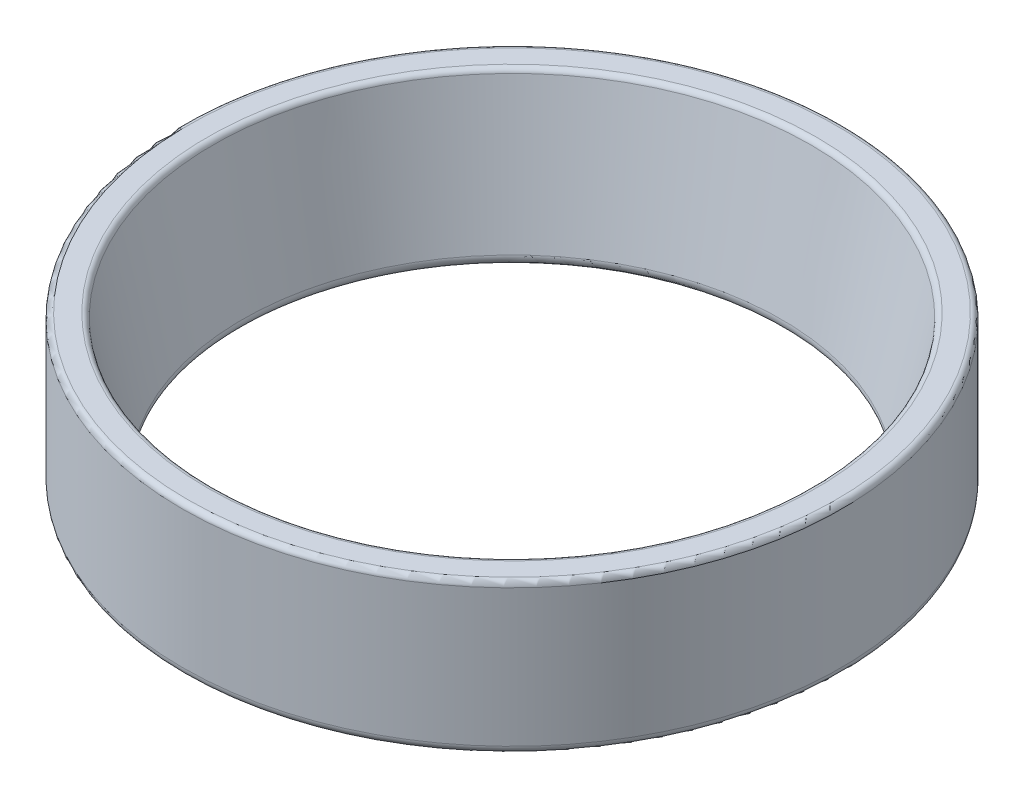
SolidWorks part; units mm, degrees
ref_plane "Front Plane" through (0, 0, 0) normal (0, 0, 1) x (1, 0, 0)
ref_plane "Top Plane" through (0, 0, 0) normal (0, 1, 0) x (1, 0, 0)
ref_plane "Right Plane" through (0, 0, 0) normal (1, 0, 0) x (0, 0, -1)
sketch "Sketch2" plane through (0, 0, 0) normal (0, 0, 1) x (1, 0, 0)
  line L0 (0, 0) -> (-30.5, 0) construction
  line L1 (0, 0) -> (0, 30.8179) construction
  line L2 (-30.5, 0) -> (-30.5, 14)
  line L3 (-30.5, 14) -> (-27.75, 14)
  line L4 (-27.75, 14) -> (-24.75, 0)
  line L5 (-30.5, 0) -> (-24.75, 0)
  dimension "D1" = 14
  dimension "D2" = 2.75
  dimension "D3" = 30.5
  dimension "D4" = 5.75
revolve "Revolve1" add sketch "Sketch2" angle 360 about L1
fillet "Fillet1" radius 0.5 2 edges at (0, 14, -30.5) (0, 14, -27.75)
fillet "Fillet3" radius 0.8 2 edges at (0, 0, -24.75) (0, 0, -30.5)
